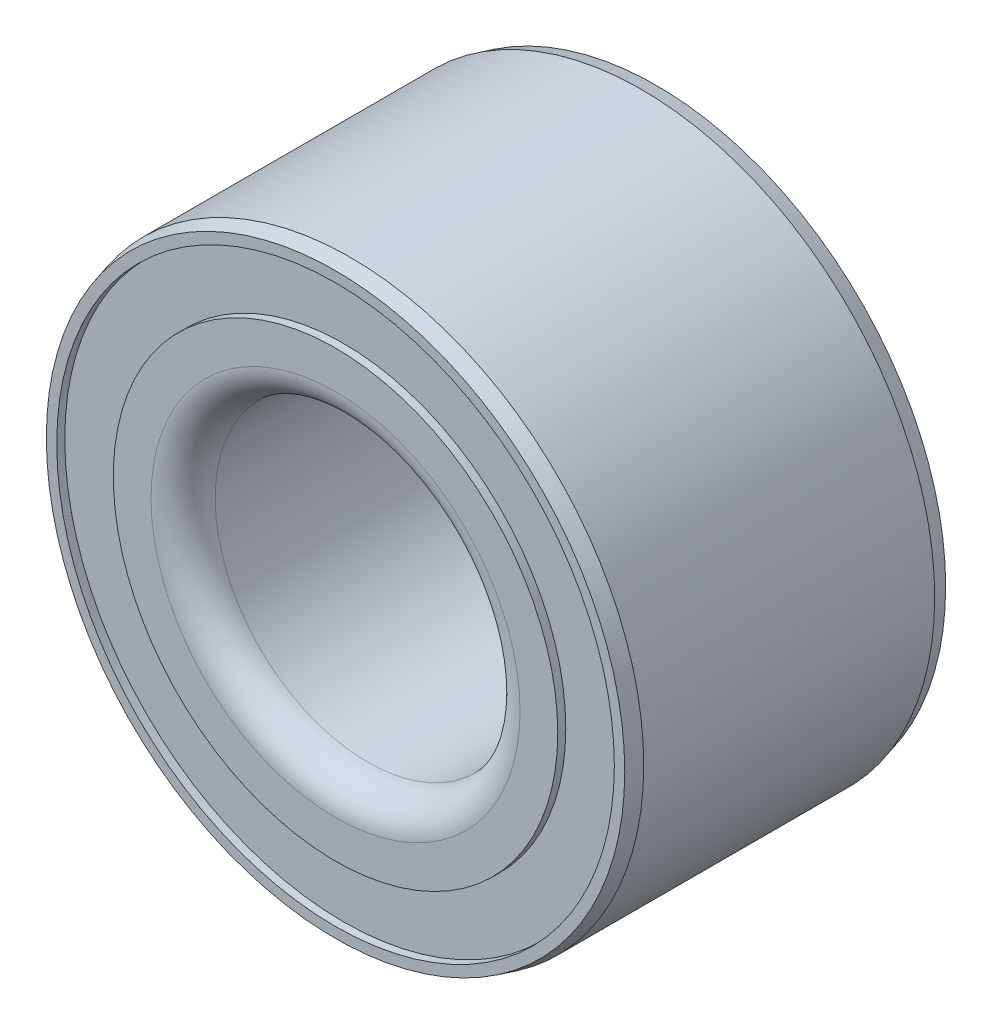
SolidWorks part; units mm, degrees
material "Plain Carbon Steel"
ref_plane "Front Plane" through (0, 0, 0) normal (0, 0, 1) x (1, 0, 0)
ref_plane "Top Plane" through (0, 0, 0) normal (0, 1, 0) x (1, 0, 0)
ref_plane "Right Plane" through (0, 0, 0) normal (1, 0, 0) x (0, 0, -1)
sketch "Sketch1" plane through (0, 0, 0) normal (0, 0, 1) x (1, 0, 0)
  circle A0 centre (0, 0) radius 36.55
  circle A1 centre (0, 0) radius 19
  dimension "D1" = 73.1
  dimension "D2" = 38
extrude "Extrude1" add sketch "Sketch1" along normal blind 40
sketch "Sketch2" plane through (0, 0, 40) normal (0, 0, 1) x (1, 0, 0)
  circle A0 centre (0, 0) radius 34.75
  circle A1 centre (0, 0) radius 27.7
  dimension "D1" = 55.4
  dimension "D2" = 69.5
extrude "Extrude2" cut sketch "Sketch2" against normal blind 1
sketch "Sketch3" plane through (0, 0, 0) normal (0, 0, -1) x (-1, 0, 0)
  circle A0 centre (0, 0) radius 27.7
  circle A1 centre (0, 0) radius 34.75
extrude "Extrude3" cut sketch "Sketch3" against normal blind 1
fillet "Fillet1" radius 4 2 edges at (19, 0, 40) (19, 0, 0)
chamfer "Chamfer1" distance 0.5 angle 75 2 edges at (36.55, 0, 40) (36.55, 0, 0)
sketch "Sketch4" plane through (0, 0, 0) normal (1, 0, 0) x (0, 0, -1)
  line L0 (8.5712, 0) -> (-46.7707, 0) construction
move or copy body "Body-Move/Copy1" [suppressed] bodies to move or copy 103
